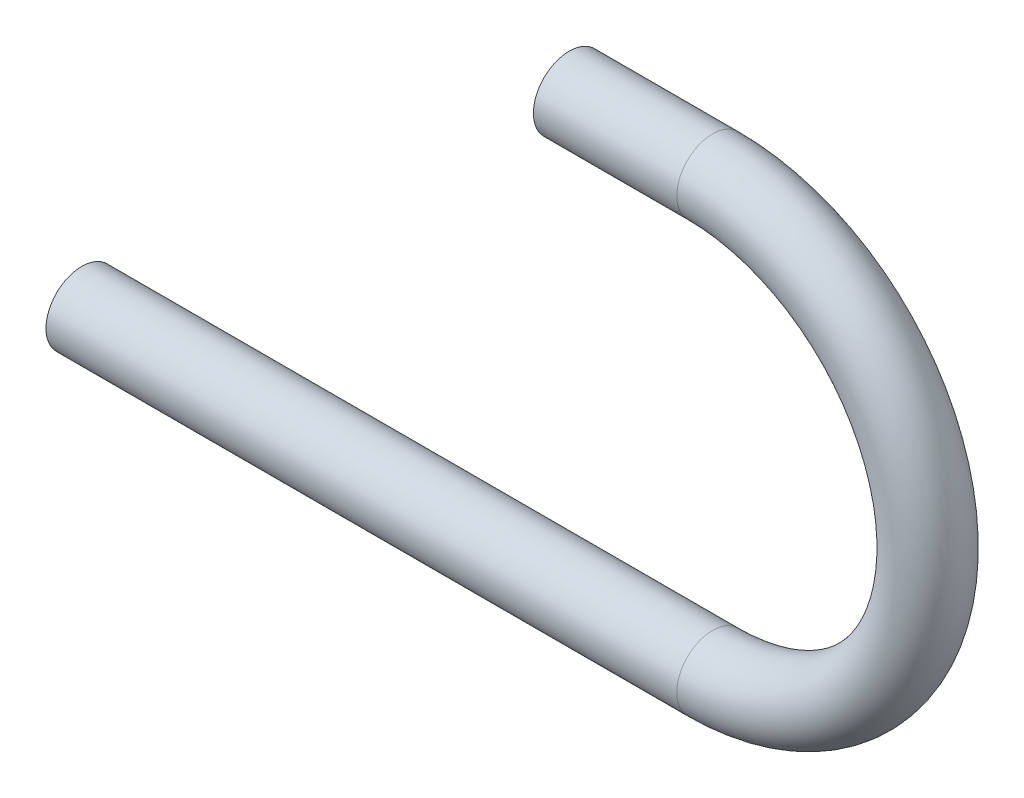
SolidWorks part; units mm, degrees
ref_plane "Front Plane" through (0, 0, 0) normal (0, 0, 1) x (1, 0, 0)
ref_plane "Top Plane" through (0, 0, 0) normal (0, 1, 0) x (1, 0, 0)
ref_plane "Right Plane" through (0, 0, 0) normal (1, 0, 0) x (0, 0, -1)
sketch "Sketch1" plane through (0, 0, 0) normal (0, 0, 1) x (1, 0, 0)
  line L0 (-6.8526, 34.4612) -> (18.5474, 34.4612)
  line L1 (18.5474, -41.7388) -> (-93.2126, -41.7388)
  arc A0 (18.5474, 34.4612) -> (18.5474, -41.7388) centre (18.5474, -3.6388) cw
  dimension "D1" = 38.1
  dimension "D2" = 25.4
  dimension "D3" = 111.76
ref_plane "Plane1" through (-6.8526, 34.4612, 0) normal (1, 0, 0) x (0, 0, -1)
sketch "Sketch2" plane through (-6.8526, 34.4612, 0) normal (1, 0, 0) x (0, 0, -1)
  line L0 (0, 0) -> (0, -76.2) construction
  circle A0 centre (0, 0) radius 6.35
  circle A1 centre (0, 0) radius 5.588
  dimension "D1" = 11.176
  dimension "D2" = 12.7
sweep "Sweep1" add profiles "Sketch2" path "Sketch1"
